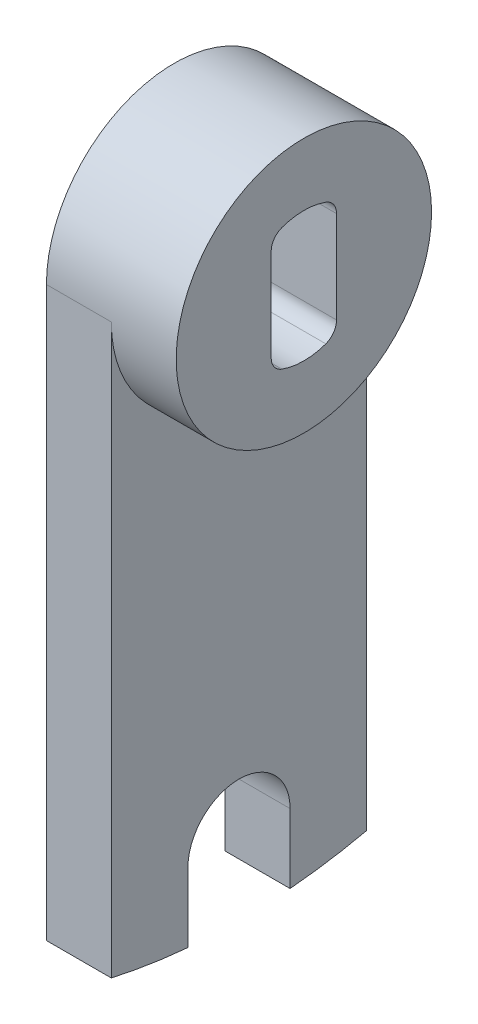
SolidWorks part; units mm, degrees
material "6061-T6 (SS)"
ref_plane "Front Plane" through (0, 0, 0) normal (0, 0, 1) x (1, 0, 0)
ref_plane "Top Plane" through (0, 0, 0) normal (0, 1, 0) x (1, 0, 0)
ref_plane "Right Plane" through (0, 0, 0) normal (1, 0, 0) x (0, 0, -1)
sketch "Sketch1" plane through (0, 0, 0) normal (1, 0, 0) x (0, 0, -1)
  line L0 (0, 0) -> (0, -21.2442) construction
  line L1 (0, 0) -> (0, -50) construction
  line L2 (12.5, 0) -> (12.5, -55.6125)
  line L3 (-12.5, 0) -> (-12.5, -55.6125)
  line L4 (-5, -50) -> (-5, -56.7803)
  line L5 (5, -50) -> (5, -56.7803)
  line L6 (-3.2004, 5.5139) -> (-3.2004, -5.5139)
  line L7 (3.2004, 5.5139) -> (3.2004, -5.5139)
  line L8 (-12.5, 0) -> (12.5, 0) construction
  arc A0 (-3.2004, -5.5139) -> (3.2004, -5.5139) centre (0, 0) ccw
  circle A1 centre (0, -50) radius 4.7879 construction
  arc A2 (12.5, 0) -> (-12.5, 0) centre (0, 0) ccw
  arc A3 (5, -56.7803) -> (12.5, -55.6125) centre (0, 0) ccw
  arc A4 (5, -50) -> (-5, -50) centre (0, -50) ccw
  arc A5 (-12.5, -55.6125) -> (-5, -56.7803) centre (0, 0) ccw
  arc A6 (3.2004, 5.5139) -> (-3.2004, 5.5139) centre (0, 0) ccw
  dimension "D1" = 12.7508
  dimension "D2" = 9.5758
  dimension "D5" = 10
  dimension "D6" = 12.5
  dimension "D7" = 114
  dimension "D3" = 50
  dimension "D4" = 25
  dimension "D8" = 6.4008
extrude "Boss-Extrude1" add sketch "Sketch1" along normal mid plane 6.35
sketch "Sketch2" plane through (3.175, 0, 0) normal (1, 0, 0) x (0, 0, -1)
  line L1 (-3.2004, 5.5139) -> (-3.2004, -5.5139) construction
  line L3 (-3.2004, 5.5139) -> (-3.2004, -5.5139)
  line L4 (3.2004, -5.5139) -> (3.2004, 5.5139) construction
  line L5 (3.2004, -5.5139) -> (3.2004, 5.5139)
  arc A0 (-3.2004, -5.5139) -> (3.2004, -5.5139) centre (0, 0) ccw
  circle A1 centre (0, 0) radius 12.5
  arc A2 (12.5, 0) -> (-12.5, 0) centre (0, 0) ccw construction
  circle A3 centre (0, 0) radius 6.3754 construction
  arc A4 (3.2004, 5.5139) -> (-3.2004, 5.5139) centre (0, 0) ccw
extrude "Boss-Extrude2" add sketch "Sketch2" along normal blind 6.35
fillet "Fillet1" radius 1.5875 4 edges at (3.175, -5.5139, 3.2004) (3.175, -5.5139, -3.2004) (3.175, 5.5139, 3.2004) (3.175, 5.5139, -3.2004)
